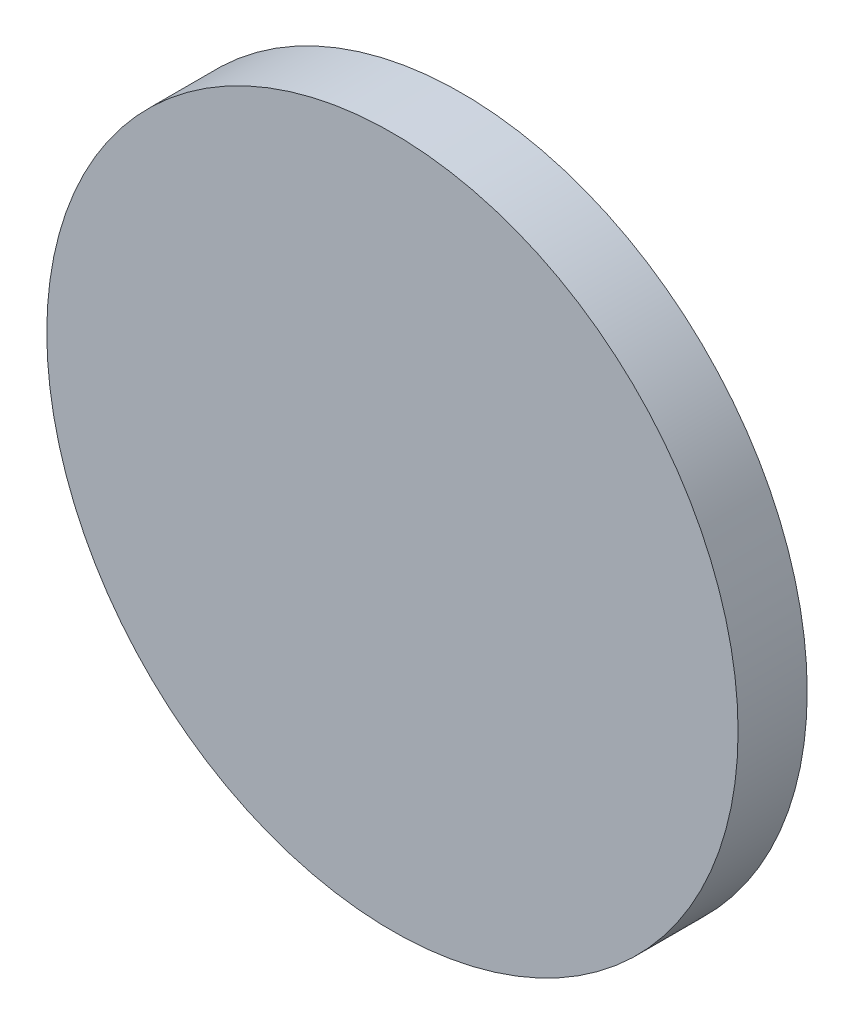
SolidWorks part; units mm, degrees
ref_plane "前视基准面" through (0, 0, 0) normal (0, 0, 1) x (1, 0, 0)
ref_plane "上视基准面" through (0, 0, 0) normal (0, 1, 0) x (1, 0, 0)
ref_plane "右视基准面" through (0, 0, 0) normal (1, 0, 0) x (0, 0, -1)
sketch "草图1" plane through (0, 0, 0) normal (0, 0, 1) x (1, 0, 0)
  circle A0 centre (0, 0) radius 25
  dimension "D1" = 50
extrude "凸台-拉伸1" add sketch "草图1" along normal blind 5 contours A0
